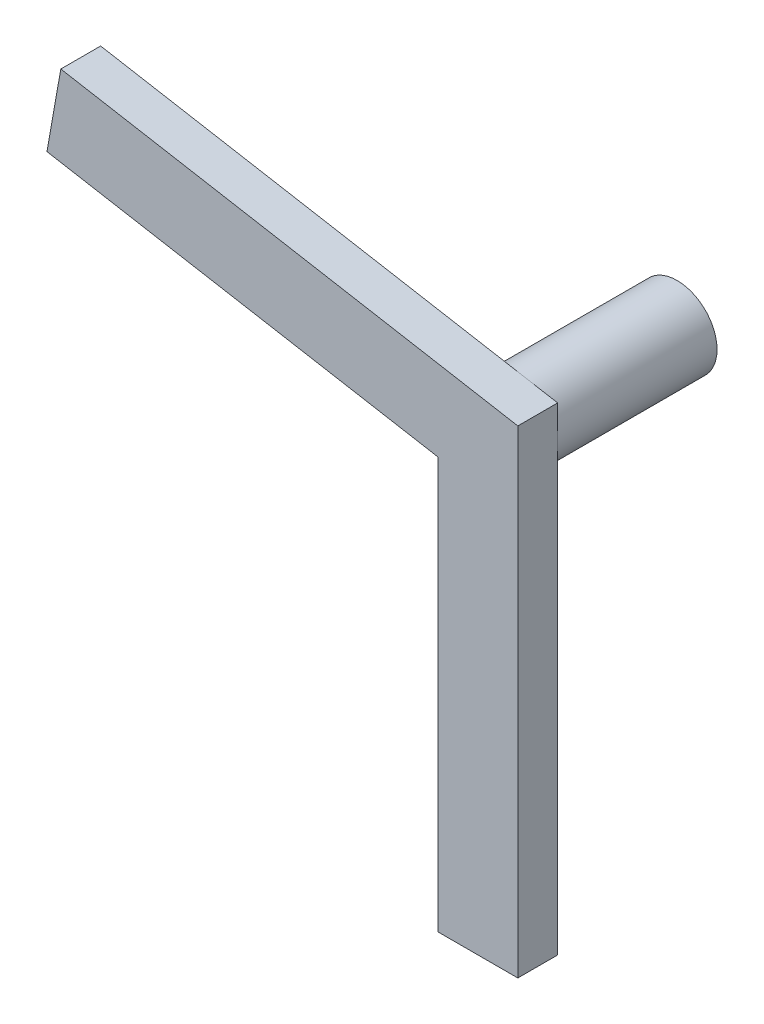
SolidWorks part; units mm, degrees
ref_plane "Plan de face" through (0, 0, 0) normal (0, 0, 1) x (1, 0, 0)
ref_plane "Plan de dessus" through (0, 0, 0) normal (0, 1, 0) x (1, 0, 0)
ref_plane "Plan de droite" through (0, 0, 0) normal (1, 0, 0) x (0, 0, -1)
sketch "Esquisse1" plane through (0, 0, 0) normal (0, 0, 1) x (1, 0, 0)
  line L0 (0, -52.4224) -> (0, 0) construction
  line L1 (0, 0) -> (-70.8588, 12.4943) construction
  line L2 (-54.0885, 4.4601) -> (-52.352, 14.3082)
  line L3 (-52.352, 14.3082) -> (5, 4.1955)
  line L6 (5, -5.9588) -> (-54.0885, 4.4601)
  line L9 (-5, -4.1955) -> (-5, -55.8045)
  line L10 (-5, -55.8045) -> (5, -55.8045)
  line L11 (5, 4.1955) -> (5, -55.8045)
  dimension "D1" = 100
  dimension "D2" = 60
  dimension "D3" = 10
  dimension "D4" = 10
  dimension "D5" = 60
  dimension "D6" = 5
  dimension "D7" = 5
extrude "Boss.-Extru.1" add sketch "Esquisse1" along normal blind 5 contours L9 L3 L2 L6 | L11 L3 L9 L6 | L11 L6 L9 L10
sketch "Esquisse2" plane through (0, 0, 0) normal (0, 0, -1) x (-1, 0, 0)
  circle A0 centre (0, 0) radius 5
  dimension "D1" = 10
extrude "Boss.-Extru.2" add sketch "Esquisse2" along normal blind 20
